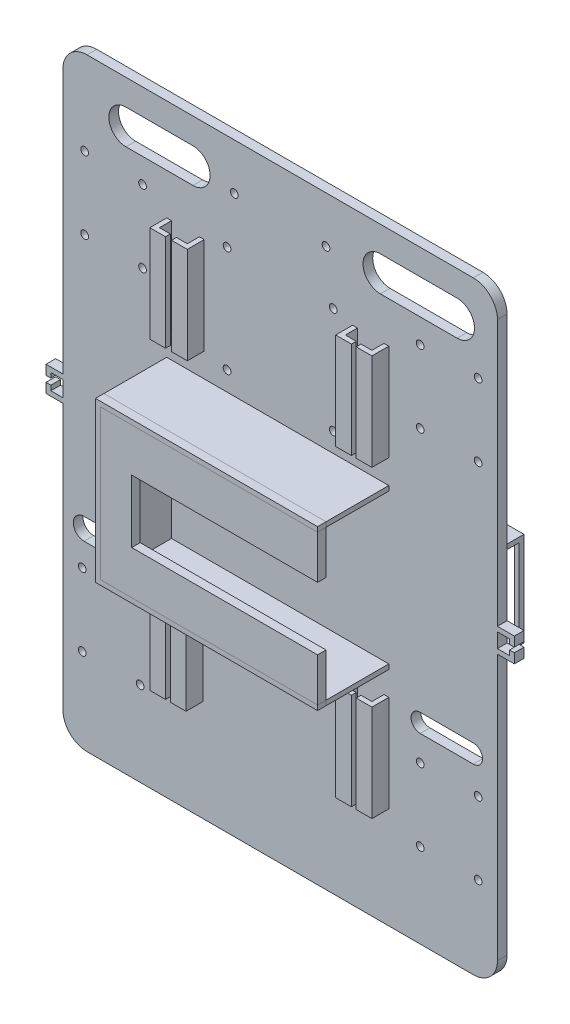
SolidWorks part; units mm, degrees
ref_plane "前视基准面" through (0, 0, 0) normal (0, 0, 1) x (1, 0, 0)
ref_plane "上视基准面" through (0, 0, 0) normal (0, 1, 0) x (1, 0, 0)
ref_plane "右视基准面" through (0, 0, 0) normal (1, 0, 0) x (0, 0, -1)
sketch "草图2" plane through (0, 0, 0) normal (0, 0, 1) x (1, 0, 0)
  line L0 (-107.1807, -135.5134) -> (-66.1807, -135.5134) construction
  line L1 (-97.1807, 63.077) -> (62.8193, 63.077)
  line L2 (-107.1807, 53.077) -> (-107.1807, -176.923)
  line L3 (-97.1807, -186.923) -> (62.8193, -186.923)
  line L4 (72.8193, 53.077) -> (72.8193, -176.923)
  line L5 (-92.3948, -186.923) -> (-92.3948, -116.923) construction
  line L6 (-85.9477, -186.923) -> (-85.9477, -156.923) construction
  line L7 (-107.1807, -156.923) -> (-66.1807, -156.923) construction
  line L8 (-107.1807, -116.923) -> (-66.1807, -116.923) construction
  line L9 (-66.1807, -116.923) -> (-66.1807, -156.923) construction
  line L10 (-66.1807, -156.923) -> (-107.1807, -156.923) construction
  line L11 (-107.1807, -156.923) -> (-107.1807, -116.923) construction
  line L12 (-107.1807, -156.923) -> (-107.1807, -158.923) construction
  line L13 (-107.1807, -152.2152) -> (-99.1807, -152.2152) construction
  line L14 (-99.1807, -156.923) -> (-99.1807, -151.923) construction
  line L15 (-99.1807, -151.923) -> (-99.1807, -121.923) construction
  line L16 (-99.1807, -121.923) -> (-75.1807, -121.923) construction
  line L17 (-75.1807, -121.923) -> (-75.1807, -151.923) construction
  line L18 (-66.1807, -156.923) -> (72.8193, -156.923) construction
  line L19 (-99.1807, -151.923) -> (72.8193, -151.923) construction
  line L20 (-99.1807, -121.923) -> (72.8193, -121.923) construction
  line L21 (72.8193, -151.923) -> (64.8193, -151.923) construction
  line L22 (64.8193, -151.923) -> (40.8193, -151.923) construction
  line L23 (40.8193, -151.923) -> (40.8193, -121.923) construction
  line L24 (40.8193, -121.923) -> (64.8193, -121.923) construction
  line L25 (64.8193, -121.923) -> (64.8193, -151.923) construction
  line L26 (-97.1807, 63.077) -> (-97.1807, 33.077) construction
  line L27 (-97.1807, 33.077) -> (-97.1807, -6.923) construction
  line L28 (-107.1807, 33.077) -> (-98.1807, 33.077) construction
  line L29 (-98.1807, 33.077) -> (-98.1807, 28.077) construction
  line L30 (-98.1807, 28.077) -> (-98.1807, -1.923) construction
  line L31 (-98.1807, 28.077) -> (-74.1807, 28.077) construction
  line L32 (-74.1807, 28.077) -> (-74.1807, -1.923) construction
  line L33 (-98.1807, -1.923) -> (-74.1807, -1.923) construction
  line L34 (-74.1807, 28.077) -> (72.8193, 28.077) construction
  line L35 (-74.1807, -1.923) -> (72.8193, -1.923) construction
  line L36 (40.8193, -121.923) -> (40.8193, 28.077) construction
  line L37 (64.8193, -121.923) -> (64.8193, 28.077) construction
  arc A0 (-97.1807, 63.077) -> (-107.1807, 53.077) centre (-97.1807, 53.077) ccw
  arc A1 (62.8193, 63.077) -> (72.8193, 53.077) centre (62.8193, 53.077) cw
  arc A2 (-107.1807, -176.923) -> (-97.1807, -186.923) centre (-97.1807, -176.923) ccw
  arc A3 (62.8193, -186.923) -> (72.8193, -176.923) centre (62.8193, -176.923) ccw
  circle A5 centre (-99.1807, -151.923) radius 1.6
  circle A6 centre (-99.1807, -121.923) radius 1.6
  circle A7 centre (-75.1807, -121.923) radius 1.6
  circle A8 centre (-75.1807, -151.923) radius 1.6
  circle A9 centre (64.8193, -151.923) radius 1.6
  circle A10 centre (40.8193, -151.923) radius 1.6
  circle A11 centre (40.8193, -121.923) radius 1.6
  circle A12 centre (64.8193, -121.923) radius 1.6
  circle A13 centre (-98.1807, 28.077) radius 1.6
  circle A14 centre (-98.1807, -1.923) radius 1.6
  circle A15 centre (-74.1807, 28.077) radius 1.6
  circle A16 centre (-74.1807, -1.923) radius 1.6
  circle A17 centre (40.8193, 28.077) radius 1.6
  circle A18 centre (64.8193, 28.077) radius 1.6
  circle A19 centre (40.8193, -1.923) radius 1.6
  circle A20 centre (64.8193, -1.923) radius 1.6
  point P6 (-107.1807, 63.077)
  point P9 (72.8193, 63.077)
  point P12 (-107.1807, -186.923)
  dimension "D3" = 10
  dimension "D4" = 10
  dimension "D5" = 10
  dimension "D6" = 10
  dimension "D13" = 30
  dimension "D14" = 24
  dimension "D15" = 8
  dimension "D16" = 24
  dimension "D17" = 30
  dimension "D21" = 30
  dimension "D22" = 24
  dimension "D1" = 180
  dimension "D2" = 250
  dimension "D7" = 41
  dimension "D8" = 70
  dimension "D9" = 30
  dimension "D10" = 41
  dimension "D11" = 8
  dimension "D12" = 5
  dimension "D18" = 40
  dimension "D19" = 9
  dimension "D20" = 5
extrude "凸台-拉伸1" add sketch "草图2" along normal blind 4
sketch "草图3" plane through (0, 0, 4) normal (0, 0, 1) x (1, 0, 0)
  line L0 (-17.1807, 63.077) -> (-17.1807, -186.923) construction
  line L1 (62.8193, 63.077) -> (-97.1807, 63.077) construction
  line L2 (-97.1807, -186.923) -> (62.8193, -186.923) construction
  line L3 (-107.1807, -61.923) -> (72.8193, -61.923) construction
  line L4 (-107.1807, 53.077) -> (-107.1807, -176.923) construction
  line L5 (72.8193, -176.923) -> (72.8193, 53.077) construction
  line L6 (-17.1807, -61.923) -> (-17.1807, -30.923) construction
  line L7 (-17.1807, -61.923) -> (-17.1807, -92.923) construction
  line L8 (-17.1807, -61.923) -> (27.8193, -61.923) construction
  line L9 (-17.1807, -61.923) -> (-62.1807, -61.923) construction
  line L10 (-17.1807, -30.923) -> (27.8193, -30.923) construction
  line L11 (27.8193, -30.923) -> (27.8193, -92.923) construction
  line L12 (27.8193, -92.923) -> (-62.1807, -92.923) construction
  line L13 (-62.1807, -92.923) -> (-62.1807, -30.923) construction
  line L14 (-62.1807, -30.923) -> (-17.1807, -30.923) construction
  line L15 (27.8193, -30.923) -> (-62.1807, -30.923)
  line L16 (-62.1807, -30.923) -> (-62.1807, -92.923)
  line L17 (-62.1807, -92.923) -> (27.8193, -92.923)
  line L18 (27.8193, -30.923) -> (27.8193, -28.923) construction
  line L19 (-62.1807, -30.923) -> (-64.1807, -30.923) construction
  line L20 (-62.1807, -92.923) -> (-62.1807, -94.923) construction
  line L21 (27.8193, -30.923) -> (27.8193, -28.923)
  line L22 (27.8193, -28.923) -> (-64.1807, -28.923)
  line L23 (-64.1807, -28.923) -> (-64.1807, -94.923)
  line L24 (-64.1807, -94.923) -> (27.8193, -94.923)
  line L25 (27.8193, -94.923) -> (27.8193, -92.923)
  dimension "D1" = 31
  dimension "D2" = 45
  dimension "D3" = 45
  dimension "D4" = 2
  dimension "D5" = 2
extrude "凸台-拉伸2" add sketch "草图3" along normal blind 26 contours L22 L23 L24 L25 L17 L16 L15 L21
sketch "草图5" plane through (0, 0, 30) normal (0, 0, 1) x (1, 0, 0)
  line L0 (-18.1807, -28.923) -> (-18.1807, -48.923) construction
  line L1 (27.8193, -28.923) -> (-64.1807, -28.923) construction
  line L2 (-18.1807, -94.923) -> (-18.1807, -74.923) construction
  line L3 (-64.1807, -94.923) -> (27.8193, -94.923) construction
  line L4 (27.8193, -28.923) -> (27.8193, -48.923)
  line L5 (27.8193, -48.923) -> (-64.1807, -48.923)
  line L6 (-64.1807, -28.923) -> (-64.1807, -94.923) construction
  line L7 (-64.1807, -48.923) -> (-64.1807, -28.923)
  line L8 (-64.1807, -28.923) -> (27.8193, -28.923)
  line L9 (27.8193, -94.923) -> (27.8193, -74.923)
  line L10 (27.8193, -74.923) -> (-64.1807, -74.923)
  line L11 (-64.1807, -28.923) -> (-64.1807, -94.923) construction
  line L12 (-64.1807, -74.923) -> (-64.1807, -94.923)
  line L13 (-64.1807, -94.923) -> (27.8193, -94.923)
  line L14 (-64.1807, -61.923) -> (-49.1807, -61.923) construction
  line L15 (-64.1807, -48.923) -> (-64.1807, -74.923)
  line L16 (-49.1807, -74.923) -> (-49.1807, -48.923)
  line L17 (-49.1807, -48.923) -> (-64.1807, -48.923)
  line M11 (27.8193, -92.923) -> (-62.1807, -92.923)
  line M12 (-62.1807, -92.923) -> (-62.1807, -30.923)
  line M13 (-62.1807, -30.923) -> (27.8193, -30.923)
  dimension "D1" = 15
extrude "凸台-拉伸3" add sketch "草图5" along normal blind 3.5 separate body contours L5 L4 M13 M12 | L9 L10 M12 M11 | L10 L16 L5 M12
sketch "草图6" plane through (0, 0, 33.5) normal (0, 0, 1) x (1, 0, 0)
  line L0 (27.8193, -30.923) -> (27.8193, -28.923)
  line L1 (27.8193, -28.923) -> (-64.1807, -28.923)
  line L2 (-64.1807, -28.923) -> (-64.1807, -94.923)
  line L3 (-64.1807, -94.923) -> (27.8193, -94.923)
  line L4 (27.8193, -94.923) -> (27.8193, -92.923)
  line L5 (27.8193, -92.923) -> (-62.1807, -92.923)
  line L6 (-62.1807, -92.923) -> (-62.1807, -30.923)
  line L7 (-62.1807, -30.923) -> (27.8193, -30.923)
extrude "凸台-拉伸4" add sketch "草图6" against normal blind 3.5 separate body
sketch "草图7" plane through (0, 0, 4) normal (0, 0, 1) x (1, 0, 0)
  line L0 (-64.1807, -94.923) -> (-64.1807, -104.923) construction
  line L1 (27.8193, -94.923) -> (27.8193, -104.923) construction
  line L2 (-64.1807, -104.923) -> (-64.1807, -144.923) construction
  line L3 (27.8193, -104.923) -> (27.8193, -144.923) construction
  line L4 (-64.1807, -104.923) -> (-62.1807, -104.923) construction
  line L5 (-62.1807, -104.923) -> (-62.1807, -144.923) construction
  line L6 (-62.1807, -144.923) -> (-64.1807, -144.923) construction
  line L7 (-64.1807, -144.923) -> (-64.1807, -104.923) construction
  line L8 (27.8193, -104.923) -> (25.8193, -104.923) construction
  line L9 (25.8193, -104.923) -> (25.8193, -144.923) construction
  line L10 (25.8193, -144.923) -> (27.8193, -144.923) construction
  line L11 (27.8193, -144.923) -> (27.8193, -104.923) construction
  line L12 (-64.1807, -104.923) -> (-49.1807, -104.923) construction
  line L13 (-49.1807, -104.923) -> (-49.1807, -144.923) construction
  line L14 (-49.1807, -144.923) -> (-51.1807, -144.923) construction
  line L15 (-51.1807, -144.923) -> (-51.1807, -104.923) construction
  line L16 (27.8193, -104.923) -> (12.8193, -104.923) construction
  line L17 (12.8193, -104.923) -> (12.8193, -144.923) construction
  line L18 (12.8193, -144.923) -> (27.8193, -144.923) construction
  line L19 (12.8193, -104.923) -> (14.8193, -104.923) construction
  line L20 (14.8193, -104.923) -> (14.8193, -144.923) construction
  line L21 (-64.1807, -104.923) -> (-62.1807, -104.923)
  line L22 (-62.1807, -104.923) -> (-62.1807, -144.923)
  line L23 (-62.1807, -144.923) -> (-64.1807, -144.923)
  line L24 (-64.1807, -144.923) -> (-64.1807, -104.923)
  line L25 (-51.1807, -104.923) -> (-51.1807, -144.923)
  line L26 (-51.1807, -144.923) -> (-49.1807, -144.923)
  line L27 (-49.1807, -144.923) -> (-49.1807, -104.923)
  line L28 (-49.1807, -104.923) -> (-51.1807, -104.923)
  line L29 (12.8193, -104.923) -> (12.8193, -144.923)
  line L30 (12.8193, -144.923) -> (14.8193, -144.923)
  line L31 (14.8193, -144.923) -> (14.8193, -104.923)
  line L32 (14.8193, -104.923) -> (12.8193, -104.923)
  line L33 (25.8193, -104.923) -> (27.8193, -104.923)
  line L34 (27.8193, -104.923) -> (27.8193, -144.923)
  line L35 (27.8193, -144.923) -> (25.8193, -144.923)
  line L36 (25.8193, -144.923) -> (25.8193, -104.923)
  dimension "D1" = 10
  dimension "D2" = 40
extrude "凸台-拉伸5" add sketch "草图7" along normal blind 5
sketch "草图8" plane through (0, 0, 9) normal (0, 0, 1) x (1, 0, 0)
  line L0 (-64.1807, -104.923) -> (-57.6807, -104.923)
  line L1 (-57.6807, -104.923) -> (-57.6807, -144.923)
  line L2 (-57.6807, -144.923) -> (-64.1807, -144.923)
  line L3 (-64.1807, -144.923) -> (-64.1807, -104.923)
  line L4 (-49.1807, -104.923) -> (-55.6807, -104.923)
  line L5 (-55.6807, -104.923) -> (-55.6807, -144.923)
  line L6 (-55.6807, -144.923) -> (-49.1807, -144.923)
  line L7 (-49.1807, -144.923) -> (-49.1807, -104.923)
  line L8 (12.8193, -104.923) -> (19.3193, -104.923)
  line L9 (19.3193, -104.923) -> (19.3193, -144.923)
  line L10 (19.3193, -144.923) -> (12.8193, -144.923)
  line L11 (12.8193, -144.923) -> (12.8193, -104.923)
  line L12 (27.8193, -104.923) -> (21.3193, -104.923)
  line L13 (21.3193, -144.923) -> (27.8193, -144.923)
  line L14 (27.8193, -144.923) -> (27.8193, -104.923)
  line L15 (21.3193, -104.923) -> (21.3193, -144.923)
extrude "凸台-拉伸6" add sketch "草图8" along normal blind 2
ref_plane "基准面1" through (-57.6807, -144.923, 9) normal (0, 0, -1) x (-1, 0, 0)
sketch "草图11" plane through (0, 0, 4) normal (0, 0, 1) x (1, 0, 0)
  line L0 (-64.1807, -28.923) -> (-64.1807, -18.923) construction
  line L1 (27.8193, -28.923) -> (27.8193, -18.923) construction
  line L2 (-64.1807, -18.923) -> (-64.1807, 21.077)
  line L3 (-64.1807, 21.077) -> (-62.1807, 21.077)
  line L4 (-62.1807, 21.077) -> (-62.1807, -18.923)
  line L5 (-62.1807, -18.923) -> (-64.1807, -18.923) construction
  line L6 (-64.1807, 21.077) -> (-48.649, 21.077) construction
  line L7 (-48.649, 21.077) -> (-50.649, 21.077)
  line L8 (-50.649, 21.077) -> (-50.649, -18.923)
  line L9 (-50.649, -18.923) -> (-48.649, -18.923)
  line L10 (-48.649, -18.923) -> (-48.649, 21.077)
  line L11 (27.8193, -18.923) -> (27.8193, 21.077)
  line L12 (27.8193, 21.077) -> (25.8193, 21.077)
  line L13 (25.8193, 21.077) -> (25.8193, -18.923)
  line L14 (25.8193, -18.923) -> (27.8193, -18.923)
  line L15 (27.8193, 21.077) -> (12.8193, 21.077) construction
  line L16 (12.8193, 21.077) -> (12.8193, -18.923)
  line L17 (12.8193, -18.923) -> (14.8193, -18.923)
  line L18 (14.8193, -18.923) -> (14.8193, 21.077)
  line L19 (14.8193, 21.077) -> (12.8193, 21.077)
extrude "凸台-拉伸7" add sketch "草图11" along normal blind 5 contours L10 L7 L8 L9 | L16 L17 L18 L19 | L13 L14 L11 L12
sketch "草图12" plane through (0, 0, 4) normal (0, 0, 1) x (1, 0, 0)
  line L0 (-64.1807, -28.923) -> (-64.1807, 21.077) construction
  line L1 (-64.1807, 21.077) -> (-62.1807, 21.077)
  line L2 (-62.1807, 21.077) -> (-62.1807, -18.923)
  line L3 (-62.1807, -18.923) -> (-64.1807, -18.923)
  line L4 (-64.1807, -18.923) -> (-64.1807, 21.077)
extrude "凸台-拉伸8" add sketch "草图12" along normal blind 5
sketch "草图13" plane through (0, 0, 9) normal (0, 0, 1) x (1, 0, 0)
  line L0 (-64.1807, 21.077) -> (-57.6807, 21.077)
  line L1 (-57.6807, 21.077) -> (-57.6807, -18.923)
  line L2 (-57.6807, -18.923) -> (-64.1807, -18.923)
  line L3 (-64.1807, 21.077) -> (-64.1807, -18.923) construction
  line L4 (-64.1807, -18.923) -> (-62.1807, -18.923) construction
  line L5 (-64.1807, -18.923) -> (-64.1807, 21.077)
extrude "凸台-拉伸9" add sketch "草图13" along normal blind 2
sketch "草图14" plane through (0, 0, 9) normal (0, 0, 1) x (1, 0, 0)
  line L0 (-48.649, 21.077) -> (-48.649, -18.923)
  line L1 (-48.649, -18.923) -> (-55.149, -18.923)
  line L2 (-55.149, -18.923) -> (-55.149, 21.077)
  line L3 (-55.149, 21.077) -> (-48.649, 21.077)
  line L4 (27.8193, -18.923) -> (21.3193, -18.923)
  line L5 (21.3193, -18.923) -> (21.3193, 21.077)
  line L6 (21.3193, 21.077) -> (27.8193, 21.077)
  line L7 (27.8193, 21.077) -> (27.8193, -18.923)
  line L8 (12.8193, -18.923) -> (19.3193, -18.923)
  line L9 (19.3193, -18.923) -> (19.3193, 21.077)
  line L10 (19.3193, 21.077) -> (12.8193, 21.077)
  line L11 (12.8193, 21.077) -> (12.8193, -18.923)
extrude "凸台-拉伸10" add sketch "草图14" along normal blind 2
sketch "草图16" plane through (0, 0, 0) normal (0, 0, -1) x (-1, 0, 0)
  line L0 (17.1807, 63.077) -> (17.1807, 23.077) construction
  line L1 (-62.8193, 63.077) -> (97.1807, 63.077) construction
  line L2 (17.1807, 23.077) -> (39.1807, 23.077) construction
  line L3 (17.1807, 23.077) -> (-4.8193, 23.077) construction
  line L4 (-4.8193, 23.077) -> (-4.8193, -20.923) construction
  line L5 (-4.8193, -20.923) -> (39.1807, -20.923) construction
  line L6 (39.1807, -20.923) -> (39.1807, 23.077) construction
  circle A0 centre (-4.8193, 23.077) radius 1.6
  circle A1 centre (39.1807, 23.077) radius 1.6
  circle A2 centre (39.1807, -20.923) radius 1.6
  circle A3 centre (-4.8193, -20.923) radius 1.6
extrude "切除-拉伸1" cut sketch "草图16" against normal blind 5
sketch "草图19" plane through (0, 0, 0) normal (0, 0, -1) x (-1, 0, 0)
  line L0 (-72.8193, -61.923) -> (107.1807, -61.923) construction
  line L1 (-72.8193, -176.923) -> (-72.8193, 53.077) construction
  line L2 (107.1807, 53.077) -> (107.1807, -176.923) construction
  line L3 (-72.8193, -61.923) -> (-32.7734, -61.923) construction
sketch "草图20" plane through (0, 0, 0) normal (0, 0, -1) x (-1, 0, 0)
  line L0 (-72.8193, -61.923) -> (-57.8193, -61.923) construction
  line L1 (-72.8193, -61.923) -> (107.1807, -61.923) construction
  line L2 (-57.8193, -61.923) -> (-22.8193, -61.923) construction
  line L3 (-22.8193, -61.923) -> (-22.8193, -44.423) construction
  line L4 (-22.8193, -61.923) -> (-22.8193, -79.423) construction
  line L5 (-22.8193, -79.423) -> (-57.8193, -79.423)
  line L6 (-57.8193, -79.423) -> (-57.8193, -44.423)
  line L7 (-57.8193, -44.423) -> (-22.8193, -44.423)
  line L8 (-22.8193, -44.423) -> (-22.8193, -79.423)
  line L9 (-22.8193, -44.423) -> (-22.8193, -42.423) construction
  line L10 (-57.8193, -44.423) -> (-59.8193, -44.423) construction
  line L11 (-57.8193, -79.423) -> (-57.8193, -81.423) construction
  line L12 (-22.8193, -79.423) -> (-20.8193, -79.423) construction
  line L13 (-22.8193, -42.423) -> (-59.8193, -42.423)
  line L14 (-59.8193, -42.423) -> (-59.8193, -81.423)
  line L15 (-59.8193, -81.423) -> (-20.8193, -81.423)
  line L16 (-20.8193, -81.423) -> (-20.8193, -42.423)
  line L17 (-20.8193, -42.423) -> (-22.8193, -42.423)
  dimension "D1" = 15
extrude "凸台-拉伸12" add sketch "草图20" along normal blind 20
sketch "草图21" plane through (20.8193, 0, 0) normal (-1, 0, 0) x (0, 0, 1)
  line L0 (0, -42.423) -> (0, -44.423) construction
  line L1 (0, 53.077) -> (0, -176.923) construction
  line L2 (0, -81.423) -> (0, -79.423) construction
  line L3 (0, -44.423) -> (-18, -44.423) construction
  line L4 (-18, -44.423) -> (-18, -79.423) construction
  line L5 (-18, -79.423) -> (0, -79.423) construction
  line L7 (0, -44.423) -> (-18, -44.423)
  line L8 (0, -44.423) -> (0, -79.423)
  line L9 (0, -79.423) -> (-18, -79.423)
  line L10 (-18, -44.423) -> (-18, -79.423)
extrude "切除-拉伸2" cut sketch "草图21" against normal blind 60
sketch "草图22" plane through (59.8193, 0, 0) normal (1, 0, 0) x (0, 0, -1)
  line L0 (18, -79.423) -> (0, -79.423) construction
  line L1 (0, -44.423) -> (3, -44.423)
  line L2 (0, -44.423) -> (0, -79.423)
  line L3 (0, -79.423) -> (3, -79.423)
  line L4 (3, -44.423) -> (3, -79.423)
  dimension "D1" = 3
extrude "凸台-拉伸13" add sketch "草图22" against normal blind 1
sketch "草图23" plane through (20.8193, 0, 0) normal (-1, 0, 0) x (0, 0, 1)
  line L1 (0, -44.423) -> (-3, -44.423)
  line L2 (0, -44.423) -> (0, -79.423)
  line L3 (0, -79.423) -> (-3, -79.423)
  line L4 (-3, -44.423) -> (-3, -79.423)
extrude "凸台-拉伸18" add sketch "草图23" against normal blind 1
sketch "草图24" plane through (0, 0, 0) normal (0, 0, -1) x (-1, 0, 0)
  line L0 (107.1807, -61.923) -> (92.1807, -61.923) construction
  line L1 (-72.8193, -61.923) -> (107.1807, -61.923) construction
  line L2 (92.1807, -61.923) -> (92.1807, -44.423) construction
  line L3 (92.1807, -44.423) -> (57.1807, -44.423) construction
  line L4 (57.1807, -44.423) -> (57.1807, -79.423) construction
  line L5 (57.1807, -79.423) -> (92.1807, -79.423) construction
  line L6 (92.1807, -79.423) -> (92.1807, -61.923) construction
  line L7 (92.1807, -44.423) -> (92.1807, -42.423) construction
  line L8 (92.1807, -44.423) -> (57.1807, -44.423)
  line L9 (92.1807, -44.423) -> (92.1807, -79.423)
  line L10 (92.1807, -79.423) -> (57.1807, -79.423)
  line L11 (57.1807, -44.423) -> (57.1807, -79.423)
  line L12 (92.1807, -44.423) -> (94.1807, -44.423) construction
  line L14 (93.8137, -42.423) -> (54.8137, -42.423)
  line L15 (93.8137, -42.423) -> (93.8137, -81.423)
  line L16 (93.8137, -81.423) -> (54.8137, -81.423)
  line L17 (54.8137, -42.423) -> (54.8137, -81.423)
  dimension "D1" = 39
  dimension "D2" = 39
extrude "凸台-拉伸19" add sketch "草图24" along normal blind 20
sketch "草图25" plane through (-93.8137, 0, 0) normal (-1, 0, 0) x (0, 0, 1)
  line L0 (0, -42.423) -> (-3, -42.423) construction
  line L1 (-20, -42.423) -> (0, -42.423) construction
  line L2 (0, -81.423) -> (-3, -81.423) construction
  line L3 (-20, -81.423) -> (0, -81.423) construction
  line L4 (-3, -81.423) -> (-3, -76.423) construction
  line L5 (-3, -42.423) -> (-3, -44.423) construction
  line L6 (-20, -44.423) -> (-15, -44.423)
  line L7 (-20, -76.423) -> (-15, -76.423) construction
  line L8 (-20, -81.423) -> (-20, -42.423) construction
  line L10 (-15, -44.423) -> (-3, -44.423)
  line L11 (-15, -44.423) -> (-15, -76.423)
  line L12 (-15, -76.423) -> (-3, -76.423)
  line L13 (-3, -44.423) -> (-3, -76.423)
  dimension "D1" = 5
extrude "切除-拉伸3" cut sketch "草图25" against normal blind 50 contours L13 L10 L11 L12
sketch "草图26" plane through (72.8193, 0, 0) normal (1, 0, 0) x (0, 0, -1)
  line L0 (-4, -56.923) -> (0, -56.923)
  line L1 (0, -42.423) -> (0, -81.423) construction
  line L2 (0, -176.923) -> (0, 53.077) construction
  line L3 (0, -61.923) -> (0, -66.923) construction
  line L4 (0, -56.923) -> (-4, -56.923) construction
  line L5 (-4, -176.923) -> (-4, 53.077) construction
  line L6 (-4, -56.923) -> (-4, -58.923) construction
  line L7 (0, -66.923) -> (-4, -66.923) construction
  line L8 (-4, -66.923) -> (-4, -64.923) construction
  line L9 (0, -58.923) -> (-4, -58.923)
  line L13 (0, -56.923) -> (0, -58.923)
  line L14 (0, -66.923) -> (-4, -66.923)
  line L15 (0, -66.923) -> (0, -64.923)
  line L16 (0, -64.923) -> (-4, -64.923)
  line L17 (-4, -66.923) -> (-4, -64.923)
  line L18 (-4, -58.923) -> (-4, -56.923)
extrude "凸台-拉伸20" add sketch "草图26" along normal blind 5
sketch "草图27" plane through (77.8193, 0, 0) normal (1, 0, 0) x (0, 0, -1)
  line L0 (-4, -56.923) -> (-4, -60.923)
  line L1 (-4, -64.923) -> (-4, -58.923) construction
  line L2 (-4, -60.923) -> (0, -60.923)
  line L3 (0, -64.923) -> (0, -58.923) construction
  line L4 (0, -60.923) -> (0, -56.923)
  line L5 (0, -56.923) -> (-4, -56.923)
  line L6 (-4, -66.923) -> (-4, -62.923)
  line L7 (-4, -62.923) -> (0, -62.923)
  line L8 (0, -42.423) -> (0, -81.423) construction
  line L9 (0, -62.923) -> (0, -66.923)
  line L10 (0, -66.923) -> (-4, -66.923)
extrude "凸台-拉伸21" add sketch "草图27" along normal blind 2
sketch "草图28" plane through (-107.1807, 0, 0) normal (-1, 0, 0) x (0, 0, 1)
  line L0 (0, -61.923) -> (0, -56.402) construction
  line L2 (0, -81.423) -> (0, -42.423) construction
  line L3 (0, -61.923) -> (0, -66.923) construction
  line L4 (0, -56.402) -> (0, -58.402)
  line L5 (0, -58.402) -> (4, -58.402)
  line L6 (4, -28.923) -> (4, -94.923) construction
  line L7 (4, -58.402) -> (4, -56.402)
  line L8 (4, -56.402) -> (0, -56.402)
  line L9 (0, -66.923) -> (0, -64.923)
  line L10 (0, -64.923) -> (4, -64.923)
  line L11 (4, 53.077) -> (4, -176.923) construction
  line L12 (4, -64.923) -> (4, -66.923)
  line L13 (4, -66.923) -> (0, -66.923)
extrude "凸台-拉伸22" add sketch "草图28" along normal blind 5
sketch "草图29" plane through (-112.1807, 0, 0) normal (-1, 0, 0) x (0, 0, 1)
  line L0 (0, -56.402) -> (0, -60.402)
  line L1 (0, -58.402) -> (0, -64.923) construction
  line L2 (0, -60.402) -> (4, -60.402)
  line L3 (4, -58.402) -> (4, -64.923) construction
  line L4 (4, -60.402) -> (4, -56.402)
  line L5 (4, -56.402) -> (0, -56.402)
  line L6 (0, -66.923) -> (0, -62.923)
  line L7 (0, -62.923) -> (4, -62.923)
  line L8 (4, -62.923) -> (4, -66.923)
  line L9 (4, -28.923) -> (4, -94.923) construction
  line L10 (4, -66.923) -> (0, -66.923)
extrude "凸台-拉伸23" add sketch "草图29" along normal blind 2
sketch "草图31" plane through (0, 0, 0) normal (0, 0, -1) x (-1, 0, 0)
  line L0 (17.1807, 63.077) -> (17.1807, -186.923) construction
  line L1 (-62.8193, 63.077) -> (97.1807, 63.077) construction
  line L2 (97.1807, -186.923) -> (-62.8193, -186.923) construction
sketch "草图34" plane through (0, 0, 4) normal (0, 0, 1) x (1, 0, 0)
  line L0 (-98.42, -107.5663) -> (-76.2578, -107.5663) construction
  line L1 (-98.42, -103.1076) -> (-76.2578, -103.1076)
  line L2 (-98.42, -112.0249) -> (-76.2578, -112.0249)
  line L3 (40.8291, -107.5663) -> (62.8404, -107.5663) construction
  line L4 (40.8291, -103.7723) -> (62.8404, -103.7723)
  line L5 (40.8291, -111.3603) -> (62.8404, -111.3603)
  arc A0 (-98.42, -103.1076) -> (-98.42, -112.0249) centre (-98.42, -107.5663) ccw
  arc A1 (-76.2578, -112.0249) -> (-76.2578, -103.1076) centre (-76.2578, -107.5663) ccw
  arc A2 (40.8291, -103.7723) -> (40.8291, -111.3603) centre (40.8291, -107.5663) ccw
  arc A3 (62.8404, -111.3603) -> (62.8404, -103.7723) centre (62.8404, -107.5663) ccw
  point P2 (-87.3389, -107.5663)
  point P7 (51.8348, -107.5663)
extrude "切除-拉伸5" cut sketch "草图34" against normal blind 10
sketch "草图37" plane through (0, 0, 0) normal (0, 0, -1) x (-1, 0, 0)
  line L0 (17.1807, 43.8668) -> (-1.8193, 43.8668) construction
  line L1 (17.1807, 63.077) -> (17.1807, -186.923) construction
  line L2 (17.1807, 43.8668) -> (36.1807, 43.8668) construction
  circle A0 centre (-1.8193, 43.8668) radius 1.6
  circle A1 centre (36.1807, 43.8668) radius 1.6
extrude "切除-拉伸6" cut sketch "草图37" against normal blind 10
sketch "草图40" plane through (0, 0, 0) normal (0, 0, -1) x (-1, 0, 0)
  line L0 (-56.1176, 45.2727) -> (-24.3351, 45.2727) construction
  line L1 (-56.1176, 52.4564) -> (-24.3351, 52.4564)
  line L2 (-56.1176, 38.089) -> (-24.3351, 38.089)
  line L3 (53.3173, 45.2727) -> (81.0376, 45.2727) construction
  line L4 (53.3173, 52.3878) -> (81.0376, 52.3878)
  line L5 (53.3173, 38.1576) -> (81.0376, 38.1576)
  arc A0 (-56.1176, 52.4564) -> (-56.1176, 38.089) centre (-56.1176, 45.2727) ccw
  arc A1 (-24.3351, 38.089) -> (-24.3351, 52.4564) centre (-24.3351, 45.2727) ccw
  arc A2 (53.3173, 52.3878) -> (53.3173, 38.1576) centre (53.3173, 45.2727) ccw
  arc A3 (81.0376, 38.1576) -> (81.0376, 52.3878) centre (81.0376, 45.2727) ccw
  point P2 (-40.2263, 45.2727)
  point P7 (67.1775, 45.2727)
extrude "切除-拉伸7" cut sketch "草图40" against normal blind 10
